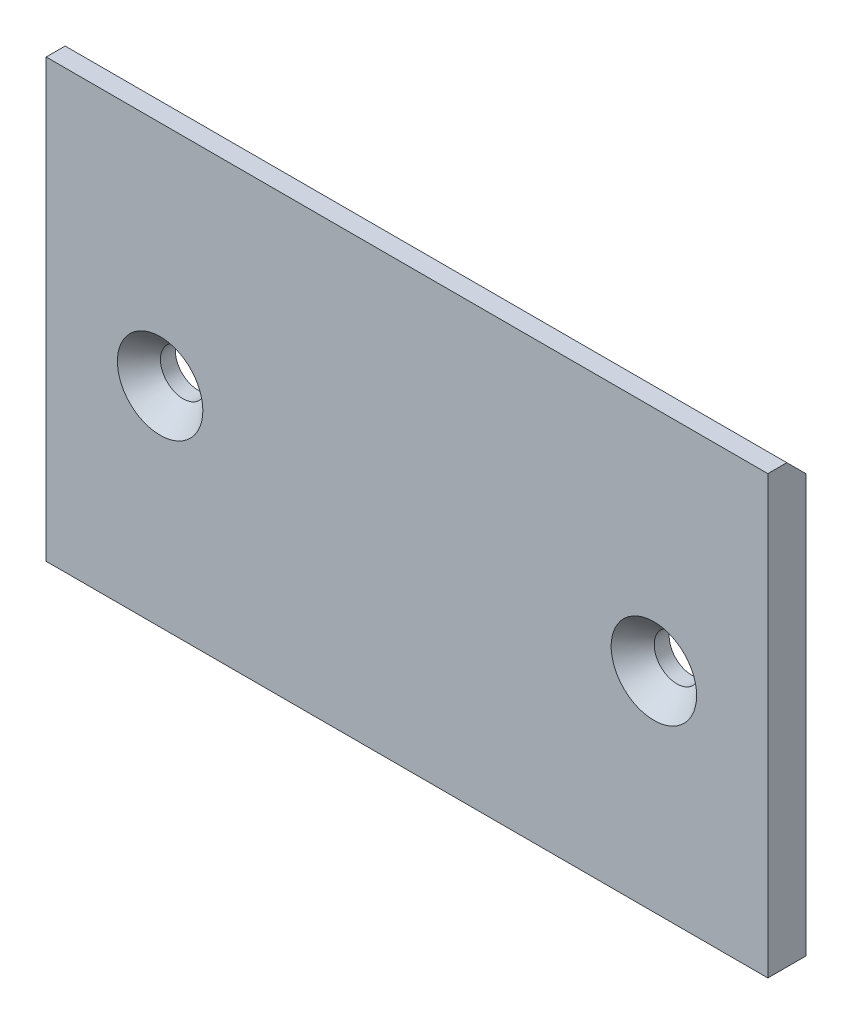
SolidWorks part; units mm, degrees
material "Chrome Stainless Steel"
ref_plane "Front Plane" through (0, 0, 0) normal (0, 0, 1) x (1, 0, 0)
ref_plane "Top Plane" through (0, 0, 0) normal (0, 1, 0) x (1, 0, 0)
ref_plane "Right Plane" through (0, 0, 0) normal (1, 0, 0) x (0, 0, -1)
sketch "Sketch1" plane through (0, 0, 0) normal (0, 0, 1) x (1, 0, 0)
  line L0 (30.1625, 18.2562) -> (-30.1625, -18.2562) construction
  line L1 (-30.1625, 18.2562) -> (30.1625, 18.2562)
  line L2 (-30.1625, 18.2562) -> (-30.1625, -18.2562)
  line L3 (-30.1625, -18.2562) -> (30.1625, -18.2562)
  line L4 (30.1625, 18.2562) -> (30.1625, -18.2562)
  point P4 (0, 0)
  dimension "D1" = 36.5125
  dimension "D2" = 60.325
extrude "Extrude1" add sketch "Sketch1" along normal mid plane 3.175
chamfer "Chamfer1" distance 1.5875 angle 45 1 edges at (0, 18.2562, -1.5875)
hole_wizard "#6 Clearance Hole1" positions "3DSketch1" profile "Sketch2" hole size "#6" standard "Ansi Inch"
sketch3d "3DSketch1"
  line L0 (-30.1625, -18.2562, 1.5875) -> (30.1625, -18.2562, 1.5875) construction
  line L1 (-30.1625, 18.2562, 1.5875) -> (-30.1625, -18.2562, 1.5875) construction
  point P0 (-20.6375, -0.7938, 1.5875)
  point P2 (20.6375, -0.7938, 1.5875)
  dimension "D1" = 17.4625
  dimension "D2" = 9.525
  dimension "D3" = 41.275
sketch "Sketch2" plane through (-20.6375, -0.7938, 1.5875) normal (1, 0, 0) x (0, -1, 0)
  line L0 (0, 0) -> (0, 26.5408)
  line L1 (0, 26.5408) -> (1.8986, 25.4)
  line L2 (1.8986, 25.4) -> (1.8986, 1.9248)
  line L3 (1.8986, 1.9248) -> (3.5719, 0)
  line L5 (3.5719, 0) -> (0, 0)
  line L6 (-1.8986, 1.9248) -> (-3.5719, 0) construction
  line L10 (0, 26.5408) -> (-1.8986, 25.4) construction
  line L11 (0, -6.35) -> (0, 107.95) construction
  dimension "Hole Dia." = 3.7973
  dimension "Hole Depth" = 25.4
  dimension "Near C'Sink Dia." = 7.1437
  dimension "Near C'Sink Angle" = 82
  dimension "Drill Angle" = 118
